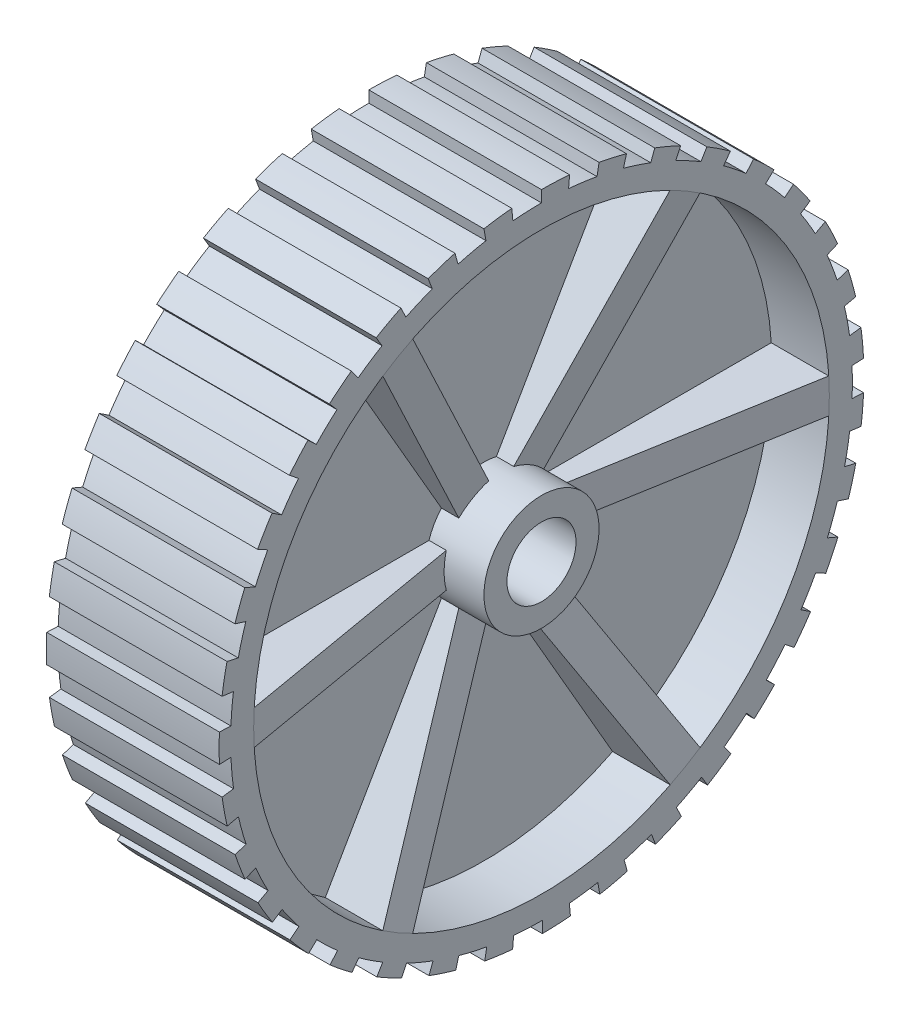
SolidWorks part; units mm, degrees
material "ABS"
ref_plane "Front Plane" through (0, 0, 0) normal (0, 0, 1) x (1, 0, 0)
ref_plane "Top Plane" through (0, 0, 0) normal (0, 1, 0) x (1, 0, 0)
ref_plane "Right Plane" through (0, 0, 0) normal (1, 0, 0) x (0, 0, -1)
sketch "Sketch1" plane through (0, 0, 0) normal (0, 0, 1) x (1, 0, 0)
  line L0 (-24.6711, 0) -> (30, 0) construction
  line L1 (2.5, 0) -> (2.5, 25)
  line L2 (2.5, 25) -> (7.5, 25)
  line L3 (7.5, 25) -> (7.5, 27)
  line L4 (7.5, 27) -> (-7.5, 27)
  line L5 (-7.5, 27) -> (-7.5, 25)
  line L6 (-7.5, 25) -> (-2.5, 25)
  line L7 (-2.5, 25) -> (-2.5, 0)
  line L8 (0, -20.4944) -> (0, 48.3463) construction
  line L9 (2.5, 0) -> (-2.5, 0)
  dimension "D1" = 15
  dimension "D2" = 2
  dimension "D3" = 25
  dimension "D4" = 5
revolve "Revolve1" add sketch "Sketch1" angle 360 about L0
sketch "Sketch2" plane through (-2.5, 0, 0) normal (-1, 0, 0) x (0, 0, 1)
  circle A0 centre (0, 0) radius 3
  dimension "D1" = 6
extrude "Cut-Extrude1" cut sketch "Sketch2" against normal through all
sketch "Sketch3" plane through (-2.5, 0, 0) normal (-1, 0, 0) x (0, 0, 1)
  circle A0 centre (0, 0) radius 3 construction
  circle A1 centre (0, 0) radius 3
  circle A2 centre (0, 0) radius 5
  dimension "D1" = 10
extrude "Boss-Extrude1" add sketch "Sketch3" along normal blind 5 and the other way blind 10
sketch "Sketch4" plane through (0, 0, 0) normal (0, 1, 0) x (1, 0, 0)
  line L0 (2.5, 5) -> (2.5, 25)
  line L1 (2.5, 25) -> (7.5, 25)
  line L2 (7.5, 25) -> (3.774, 3.4582)
  line L4 (2.5, 5) -> (2.5, 3.4582)
  line L5 (2.5, 3.4582) -> (3.774, 3.4582)
  dimension "D1" = 2
extrude "Boss-Extrude2" add sketch "Sketch4" along normal mid plane 3
pattern_circular "CirPattern1" count 6 over 360 about axis through (0, 0, 0) along (1, 0, 0) of "Boss-Extrude2"
mirror "Mirror1" about plane through (0, 0, 0) normal (1, 0, 0) of "CirPattern1", "Boss-Extrude2"
sketch "Sketch6" plane through (0, 0, 0) normal (0, 0, 1) x (1, 0, 0)
  line L0 (7.5, 27) -> (-7.5, 27) construction
  line L1 (-7.5, 28) -> (7.5, 28)
  line L2 (-7.5, 28) -> (-7.5, 26)
  line L3 (-7.5, 26) -> (7.5, 26)
  line L4 (7.5, 28) -> (7.5, 26)
  line L5 (-7.5, 28) -> (7.5, 26) construction
  line L6 (-7.5, 26) -> (7.5, 28) construction
  line L7 (7.5, -27) -> (7.5, 27) construction
  point P0 (0, 27)
  dimension "D1" = 2
revolve "Revolve2" add sketch "Sketch6" angle 5 about axis through (-24.6711, 0, 0) along (-1, 0, 0)
pattern_circular "CirPattern2" count 35 over 360 about axis through (0, 0, 0) along (1, 0, 0) of "Revolve2"
